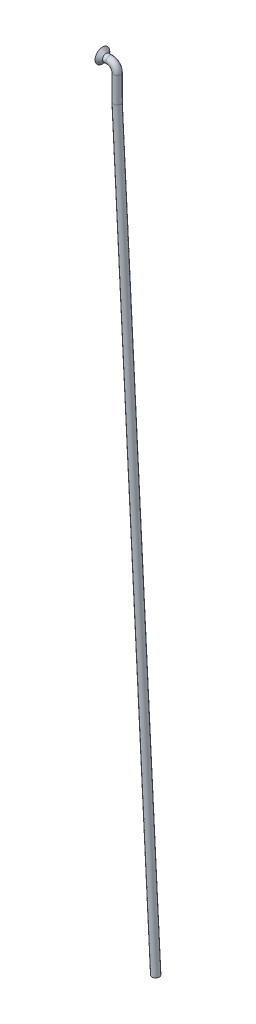
SolidWorks part; units mm, degrees
ref_plane "Plan de face" through (0, 0, 0) normal (0, 0, 1) x (1, 0, 0)
ref_plane "Plan de dessus" through (0, 0, 0) normal (0, 1, 0) x (1, 0, 0)
ref_plane "Plan de droite" through (0, 0, 0) normal (1, 0, 0) x (0, 0, -1)
sketch "Esquisse1" plane through (0, 0, 0) normal (0, 0, 1) x (1, 0, 0)
  line L1 (-2, 0) -> (-4, 0)
  line L2 (0, -2) -> (0, -9)
  line L3 (0, -9) -> (10.5201, -209.7363)
  arc A0 (0, -2) -> (-2, 0) centre (-2, -2) ccw
  point P6 (0, 0)
  dimension "D3" = 2
  dimension "D1" = 4
  dimension "D2" = 93
  dimension "D5" = 7
  dimension "D6" = 210
ref_plane "Plan1" through (-4, 0, 0) normal (1, 0, 0) x (0, 0, -1)
sketch "Esquisse2" plane through (-4, 0, 0) normal (1, 0, 0) x (0, 0, -1)
  circle A0 centre (0, 0) radius 1
  dimension "D1" = 2
sweep "Balayage1" add profiles "Esquisse2" path "Esquisse1"
sketch "Esquisse3" plane through (0, 0, 0) normal (0, 0, 1) x (1, 0, 0)
  line L0 (-4, 1) -> (-4, 2)
  line L1 (-4, 2) -> (-3, 1)
  line L2 (-3, 1) -> (-4, 1)
  line L3 (-2, 1) -> (-4, 1) construction
  line L4 (-4, 1) -> (-4, -1) construction
  line L5 (0, 0) -> (-9.5023, 0) construction
  line L6 (-2, 0) -> (-4, 0) construction
  dimension "D1" = 4
  dimension "D2" = 1
revolve "Révolution1" add sketch "Esquisse3" angle 360 about L5
